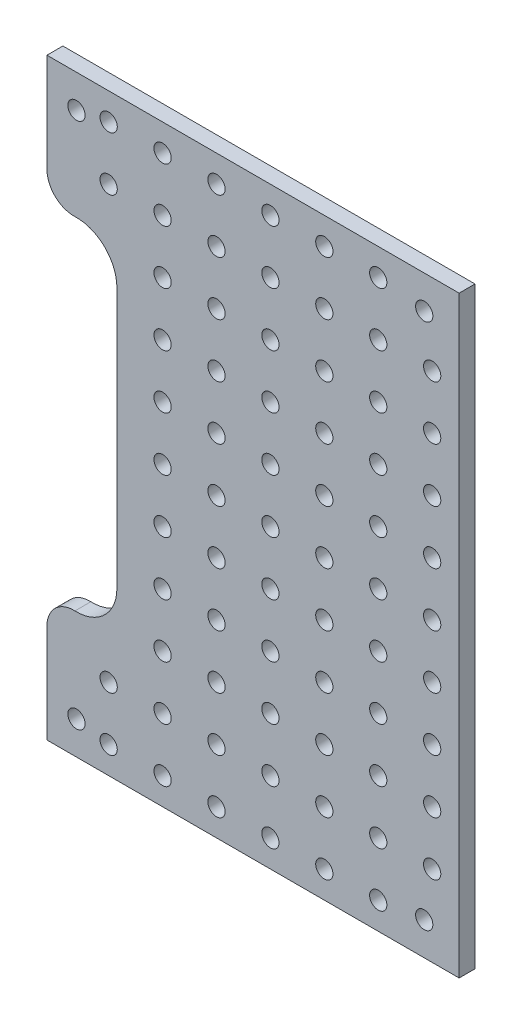
SolidWorks part; units mm, degrees
ref_plane "Front Plane" through (0, 0, 0) normal (0, 0, 1) x (1, 0, 0)
ref_plane "Top Plane" through (0, 0, 0) normal (0, 1, 0) x (1, 0, 0)
ref_plane "Right Plane" through (0, 0, 0) normal (1, 0, 0) x (0, 0, -1)
sketch "Sketch1" plane through (0, 0, 0) normal (0, 0, 1) x (1, 0, 0)
  line L0 (0.59, -55) -> (0.59, 55) construction
  line L1 (3.56, -55) -> (3.56, -29.3012)
  line L2 (6.53, 24.17) -> (6.53, -24.17)
  line L3 (11.53, -24.17) -> (11.53, 24.17)
  line L4 (80, -55) -> (80, 55)
  line L5 (80, 55) -> (-80, 55)
  line L6 (-80, 55) -> (-80, -55)
  line L7 (-80, -55) -> (80, -55)
  line L8 (80, -55) -> (80, 55)
  line L9 (80, 55) -> (-80, 55)
  line L10 (-80, 55) -> (-80, -55) construction
  line L11 (-80, -55) -> (80, -55)
  line L12 (6.53, 55) -> (6.53, -55) construction
  line L13 (11.53, -24.17) -> (11.53, 24.17) construction
  line L14 (6.53, 0) -> (0.59, 0) construction
  line L15 (16.53, -24.17) -> (16.53, 24.17)
  line L16 (3.56, 29.3012) -> (3.56, 55)
  circle A0 centre (73.525, 48.875) radius 1.6 construction
  circle A1 centre (9.03, 48.875) radius 1.6 construction
  arc A2 (11.53, 24.17) -> (6.53, 24.17) centre (9.03, 24.17) ccw
  arc A3 (6.53, -24.17) -> (11.53, -24.17) centre (9.03, -24.17) ccw
  arc A4 (11.53, 24.17) -> (6.53, 24.17) centre (9.03, 24.17) ccw construction
  arc A5 (6.53, -24.17) -> (11.53, -24.17) centre (9.03, -24.17) ccw construction
  circle A6 centre (73.525, -48.875) radius 1.6 construction
  circle A7 centre (9.03, -48.875) radius 1.6 construction
  circle A8 centre (73.525, 48.875) radius 1.6
  circle A9 centre (9.03, 48.875) radius 1.6
  circle A10 centre (73.525, -48.875) radius 1.6
  circle A11 centre (9.03, -48.875) radius 1.6
  arc A12 (3.56, -29.3012) -> (16.53, -24.17) centre (9.03, -24.17) ccw
  circle A13 centre (-1.01, 8.89) radius 1.6
  circle A14 centre (-1.01, 8.89) radius 1.6 construction
  circle A15 centre (-1.01, -19.05) radius 1.6
  circle A16 centre (-1.01, -19.05) radius 1.6 construction
  arc A17 (16.53, 24.17) -> (3.56, 29.3012) centre (9.03, 24.17) ccw
  arc A18 (1.53, -24.17) -> (16.53, -24.17) centre (9.03, -24.17) ccw construction
  arc A19 (16.53, 24.17) -> (1.53, 24.17) centre (9.03, 24.17) ccw construction
  point P23 (3.56, 0)
  dimension "D1" = 0
  dimension "D2" = 0
  dimension "D3" = 0
  dimension "D4" = 0
  dimension "D5" = 5
extrude "Boss-Extrude1" add sketch "Sketch1" along normal blind 2.95 contours A17 L15 A12 L1 L11 L8 L9 L16 A11 A10 A9 A8
fillet "Fillet1" radius 5 2 edges at (3.56, -29.3012, 1.475) (3.56, 29.3012, 1.475)
hole_wizard "M3 Clearance Hole3" positions "Sketch9" profile "Sketch10" hole size "M3" standard "ANSI Metric" end condition through all
sketch "Sketch9" plane through (0, 0, 0) normal (0, 0, -1) x (-1, 0, 0)
  line L0 (-3.56, -55) -> (-80, -55) construction
  line L1 (-80, -55) -> (-80, 55) construction
  point P0 (-15, -50)
  dimension "D1" = 5
  dimension "D2" = 65
sketch "Sketch10" plane through (15, -50, 0) normal (1, 0, 0) x (0, 1, 0)
  line L0 (0, 0) -> (0, 2.95)
  line L1 (0, 2.95) -> (1.6, 2.95)
  line L2 (1.6, 2.95) -> (1.6, 0)
  line L5 (1.6, 0) -> (0, 0)
  line L11 (0, -6.35) -> (0, 107.95) construction
  dimension "Thru Hole Dia." = 3.2
  dimension "Thru Hole Depth" = 2.95
pattern_linear "LPattern3" count 7 spacing 10 along (1, 0, 0) count 11 spacing 10 along (0, 1, 0) skipping (0, 2), (0, 3), (0, 4), (0, 5), (0, 6), (0, 7), (0, 8), (6, 0), (6, 10) of "M3 Clearance Hole3"
equation "\"wood\"= 2.95mm"
equation "\"slot_width\"= 10mm"
equation "\"slot_offset\"= 10mm"
equation "\"D1@Boss-Extrude1\"=\"wood\""
